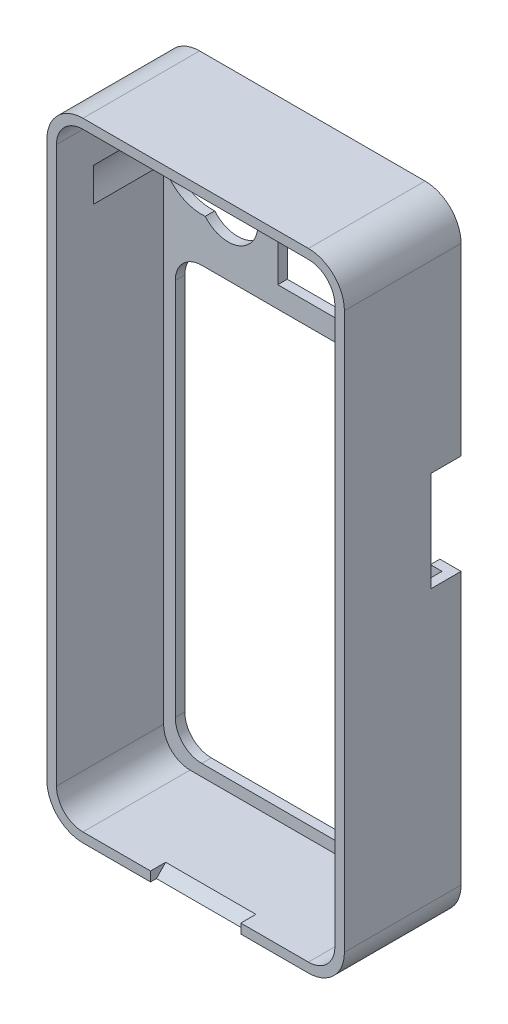
SolidWorks part; units mm, degrees
ref_plane "Front Plane" through (0, 0, 0) normal (0, 0, 1) x (1, 0, 0)
ref_plane "Top Plane" through (0, 0, 0) normal (0, 1, 0) x (1, 0, 0)
ref_plane "Right Plane" through (0, 0, 0) normal (1, 0, 0) x (0, 0, -1)
sketch "Sketch1" plane through (0, 0, 0) normal (0, 0, 1) x (1, 0, 0)
  line L12 (64.9937, 62.0139) -> (64.9937, 166.9489)
  line L13 (58.1937, 173.7489) -> (15.6157, 173.7489)
  line L14 (8.8157, 166.9489) -> (8.8157, 62.0139)
  line L15 (15.6157, 55.2139) -> (58.1937, 55.2139)
  line L20 (63.1937, 62.0139) -> (63.1937, 166.9489)
  line L21 (58.1937, 171.9489) -> (15.6157, 171.9489)
  line L22 (10.6157, 166.9489) -> (10.6157, 62.0139)
  line L23 (15.6157, 57.0139) -> (58.1937, 57.0139)
  arc A12 (58.1937, 55.2139) -> (64.9937, 62.0139) centre (58.1937, 62.0139) ccw
  arc A13 (64.9937, 166.9489) -> (58.1937, 173.7489) centre (58.1937, 166.9489) ccw
  arc A14 (15.6157, 173.7489) -> (8.8157, 166.9489) centre (15.6157, 166.9489) ccw
  arc A15 (8.8157, 62.0139) -> (15.6157, 55.2139) centre (15.6157, 62.0139) ccw
  arc A20 (58.1937, 57.0139) -> (63.1937, 62.0139) centre (58.1937, 62.0139) ccw
  arc A21 (63.1937, 166.9489) -> (58.1937, 171.9489) centre (58.1937, 166.9489) ccw
  arc A22 (15.6157, 171.9489) -> (10.6157, 166.9489) centre (15.6157, 166.9489) ccw
  arc A23 (10.6157, 62.0139) -> (15.6157, 57.0139) centre (15.6157, 62.0139) ccw
extrude "Boss-Extrude1" add sketch "Sketch1" against normal offset from surface (7 mm away) 1
sketch "Sketch2" plane through (0, 0, -7) normal (0, 0, -1) x (-1, 0, 0)
  line L4 (-58.1937, 55.2139) -> (-15.6157, 55.2139)
  line L5 (-8.8157, 62.0139) -> (-8.8157, 166.9489)
  line L6 (-15.6157, 173.7489) -> (-58.1937, 173.7489)
  line L7 (-64.9937, 166.9489) -> (-64.9937, 62.0139)
  line L8 (-58.1937, 55.2139) -> (-15.6157, 55.2139)
  line L9 (-8.8157, 62.0139) -> (-8.8157, 166.9489)
  line L10 (-15.6157, 173.7489) -> (-58.1937, 173.7489)
  line L11 (-64.9937, 166.9489) -> (-64.9937, 62.0139)
  circle A0 centre (-17.8161, 156.8686) radius 7.8755
  arc A4 (-64.9937, 62.0139) -> (-58.1937, 55.2139) centre (-58.1937, 62.0139) ccw
  arc A5 (-15.6157, 55.2139) -> (-8.8157, 62.0139) centre (-15.6157, 62.0139) ccw
  arc A6 (-8.8157, 166.9489) -> (-15.6157, 173.7489) centre (-15.6157, 166.9489) ccw
  arc A7 (-58.1937, 173.7489) -> (-64.9937, 166.9489) centre (-58.1937, 166.9489) ccw
  arc A8 (-64.9937, 62.0139) -> (-58.1937, 55.2139) centre (-58.1937, 62.0139) ccw
  arc A9 (-15.6157, 55.2139) -> (-8.8157, 62.0139) centre (-15.6157, 62.0139) ccw
  arc A10 (-8.8157, 166.9489) -> (-15.6157, 173.7489) centre (-15.6157, 166.9489) ccw
  arc A11 (-58.1937, 173.7489) -> (-64.9937, 166.9489) centre (-58.1937, 166.9489) ccw
  dimension "D1" = 0
extrude "Boss-Extrude2" add sketch "Sketch2" along normal offset from surface (15.0324 mm away) 1.8
sketch "Sketch3" plane through (0, 0, -22.0324) normal (0, 0, -1) x (-1, 0, 0)
  line L0 (-60.9937, 135.6868) -> (-60.9937, 64.2139)
  line L1 (-55.9937, 59.2139) -> (-17.8157, 59.2139)
  line L2 (-12.8157, 64.2139) -> (-12.8157, 135.6868)
  line L3 (-17.8157, 140.6868) -> (-55.9937, 140.6868)
  line L4 (-33.1793, 165.0868) -> (-61.1793, 165.0868) construction
  line L5 (-32.1793, 144.6868) -> (-61.9793, 144.6868)
  line L6 (-32.1793, 144.6868) -> (-32.1793, 165.8868)
  line L7 (-32.1793, 165.8868) -> (-61.9793, 165.8868)
  line L8 (-61.9793, 144.6868) -> (-61.9793, 165.8868)
  line L9 (-32.9793, 142.1868) -> (-32.9793, 168.5868) construction
  line L10 (-39.1793, 145.4868) -> (-33.1793, 145.4868) construction
  line L11 (-61.1793, 165.0868) -> (-61.1793, 145.4868) construction
  line L12 (-8.8157, 62.0139) -> (-8.8157, 166.9489) construction
  line L13 (-64.9937, 166.9489) -> (-64.9937, 62.0139) construction
  line L14 (-58.1937, 55.2139) -> (-15.6157, 55.2139) construction
  circle A0 centre (-22.8022, 152.6316) radius 5.636
  circle A1 centre (-22.8022, 152.6316) radius 3.35 construction
  arc A2 (-55.9937, 59.2139) -> (-60.9937, 64.2139) centre (-55.9937, 64.2139) cw
  arc A3 (-17.8157, 59.2139) -> (-12.8157, 64.2139) centre (-17.8157, 64.2139) ccw
  arc A4 (-12.8157, 135.6868) -> (-17.8157, 140.6868) centre (-17.8157, 135.6868) ccw
  arc A5 (-60.9937, 135.6868) -> (-55.9937, 140.6868) centre (-55.9937, 135.6868) cw
  dimension "D5" = 2.286
  dimension "D10" = 5
  dimension "D1" = 0.8
  dimension "D2" = 0.8
  dimension "D3" = 0.8
  dimension "D4" = 0.8
  dimension "D6" = 4
  dimension "D7" = 4
  dimension "D8" = 4
  dimension "D9" = 4
extrude "Cut-Extrude1" cut sketch "Sketch3" against normal blind 6.88
sketch "Sketch4" plane through (0, 0, -7) normal (0, 0, 1) x (1, 0, 0)
  line L4 (15.6157, 57.0139) -> (58.1937, 57.0139)
  line L5 (63.1937, 62.0139) -> (63.1937, 166.9489)
  line L6 (58.1937, 171.9489) -> (15.6157, 171.9489)
  line L7 (10.6157, 166.9489) -> (10.6157, 160.0588)
  line L8 (15.6157, 57.0139) -> (58.1937, 57.0139)
  line L9 (63.1937, 62.0139) -> (63.1937, 166.9489)
  line L10 (58.1937, 171.9489) -> (15.6157, 171.9489)
  line L11 (10.6157, 166.9489) -> (10.6157, 160.0588)
  line L13 (10.6157, 153.6784) -> (10.6157, 62.0139)
  line L14 (10.6157, 153.6784) -> (10.6157, 62.0139)
  arc A4 (10.6157, 62.0139) -> (15.6157, 57.0139) centre (15.6157, 62.0139) ccw
  arc A5 (58.1937, 57.0139) -> (63.1937, 62.0139) centre (58.1937, 62.0139) ccw
  arc A6 (63.1937, 166.9489) -> (58.1937, 171.9489) centre (58.1937, 166.9489) ccw
  arc A7 (15.6157, 171.9489) -> (10.6157, 166.9489) centre (15.6157, 166.9489) ccw
  arc A8 (10.6157, 62.0139) -> (15.6157, 57.0139) centre (15.6157, 62.0139) ccw
  arc A9 (58.1937, 57.0139) -> (63.1937, 62.0139) centre (58.1937, 62.0139) ccw
  arc A10 (63.1937, 166.9489) -> (58.1937, 171.9489) centre (58.1937, 166.9489) ccw
  arc A11 (15.6157, 171.9489) -> (10.6157, 166.9489) centre (15.6157, 166.9489) ccw
  arc A13 (10.6157, 153.6784) -> (10.6157, 160.0588) centre (17.8161, 156.8686) ccw
  arc A14 (10.6157, 153.6784) -> (10.6157, 160.0588) centre (17.8161, 156.8686) ccw
  dimension "D1" = 0
extrude "Cut-Extrude2" cut sketch "Sketch4" against normal offset from surface (13.2324 mm away) 1.8 up to face at (36.9047, 99.9503, -22.0324)
sketch "Sketch5" plane through (64.9937, 0, 0) normal (1, 0, 0) x (0, 0, -1)
  line L0 (14.3324, 59.5539) -> (14.3324, 169.4089) construction
  line L1 (16.3324, 132.1725) -> (22.8324, 132.1725)
  line L2 (16.3324, 132.1725) -> (16.3324, 113.3115)
  line L3 (16.3324, 113.3115) -> (22.8324, 113.3115)
  line L4 (22.8324, 132.1725) -> (22.8324, 113.3115)
  dimension "D1" = 6.5
  dimension "D2" = 18.8609
  dimension "D3" = 2
extrude "Cut-Extrude3" cut sketch "Sketch5" against normal blind 6.88
ref_plane "Plane1" through (36.9047, 0, 0) normal (-1, 0, 0) x (0, 0, 1)
sketch "Sketch6" plane through (36.9047, 0, 0) normal (-1, 0, 0) x (0, 0, 1)
  line L0 (0, 57.0139) -> (-2.8536, 57.0139)
  line L1 (-20.2324, 57.0139) -> (0, 57.0139) construction
  line L2 (-2.8536, 57.0139) -> (-1.108, 55.2139)
  line L3 (-22.0324, 55.2139) -> (0, 55.2139) construction
  line L4 (-1.108, 55.2139) -> (0, 55.2139)
  line L5 (0, 55.2139) -> (0, 57.0139)
extrude "Cut-Extrude4" cut sketch "Sketch6" against normal mid plane 17.04
